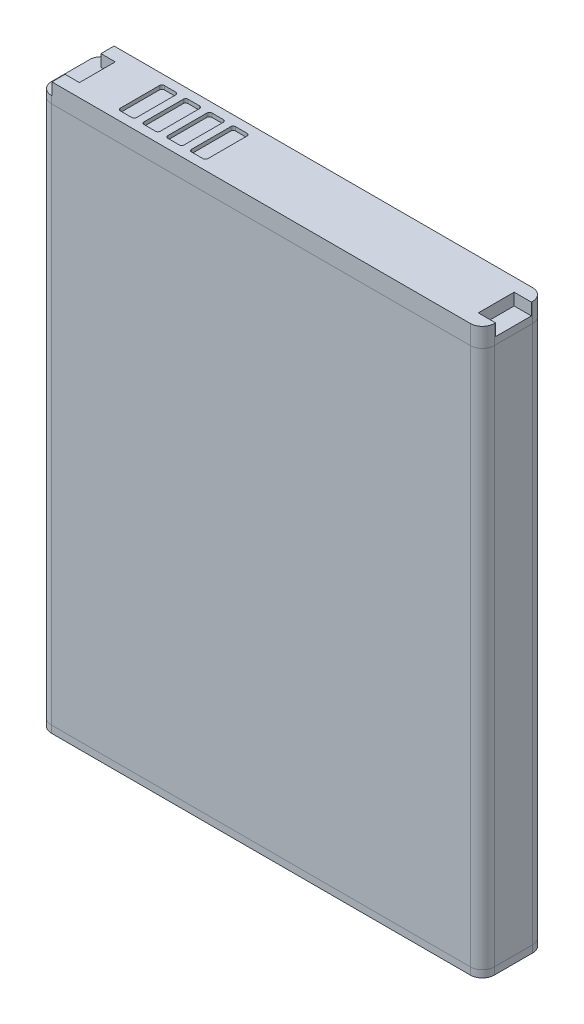
SolidWorks part; units mm, degrees
ref_plane "Front Plane" through (0, 0, 0) normal (0, 0, 1) x (1, 0, 0)
ref_plane "Top Plane" through (0, 0, 0) normal (0, 1, 0) x (1, 0, 0)
ref_plane "Right Plane" through (0, 0, 0) normal (1, 0, 0) x (0, 0, -1)
sketch "Sketch1" plane through (0, 0, 0) normal (0, 1, 0) x (1, 0, 0)
  line L1 (-23.15, -3.25) -> (23.15, -3.25)
  line L2 (-23.15, -3.25) -> (-23.15, 3.25)
  line L3 (-23.15, 3.25) -> (23.15, 3.25)
  line L4 (23.15, -3.25) -> (23.15, 3.25)
  line L5 (-23.15, -3.25) -> (23.15, 3.25) construction
  line L6 (-23.15, 3.25) -> (23.15, -3.25) construction
  point P0 (0, 0)
  dimension "D1" = 6.5
  dimension "D2" = 46.3
extrude "Boss-Extrude1" add sketch "Sketch1" along normal blind 59
fillet "Fillet1" radius 1.25 4 edges at (-23.15, 29.5, 3.25) (-23.15, 29.5, -3.25) (23.15, 29.5, -3.25) (23.15, 29.5, 3.25)
sketch "Sketch2" plane through (0, 59, 0) normal (0, 1, 0) x (1, 0, 0)
  line L0 (0, 0) -> (0, 3.25) construction
  line L1 (21.9, 3.25) -> (-21.9, 3.25) construction
  line L2 (23.15, -2) -> (23.15, 2) construction
  line L3 (21.35, -1.875) -> (23.15, -1.875)
  line L4 (21.35, -1.875) -> (21.35, 1.875)
  line L5 (21.35, 1.875) -> (23.15, 1.875)
  line L6 (23.15, -1.875) -> (23.15, 1.875)
  line L7 (21.35, -1.875) -> (23.15, 1.875) construction
  line L8 (21.35, 1.875) -> (23.15, -1.875) construction
  line L9 (-21.85, 3.25) -> (-21.85, 1.875)
  line L10 (-21.85, 1.875) -> (-20.35, 1.875)
  line L11 (-20.35, 1.875) -> (-20.35, 0)
  line L12 (-20.35, 0) -> (-20.35, -1.875)
  line L13 (-20.35, -1.875) -> (-21.85, -1.875)
  line L14 (-21.85, -1.875) -> (-21.85, -3.25)
  line L15 (-21.9, -3.25) -> (21.9, -3.25) construction
  line L16 (-23.15, 2) -> (-23.15, -2) construction
  line L17 (-21.9, -3.25) -> (-21.85, -3.25)
  line L18 (-23.15, 2) -> (-23.15, -2)
  line L19 (21.9, 3.25) -> (0, 3.25)
  line L20 (-21.85, 3.25) -> (-21.9, 3.25)
  arc A0 (-23.15, -2) -> (-21.9, -3.25) centre (-21.9, -2) ccw construction
  arc A1 (-21.9, 3.25) -> (-23.15, 2) centre (-21.9, 2) ccw construction
  arc A2 (-23.15, -2) -> (-21.9, -3.25) centre (-21.9, -2) ccw
  arc A3 (-21.9, 3.25) -> (-23.15, 2) centre (-21.9, 2) ccw
  point P4 (0, 0)
  point P5 (22.25, 0)
  point P23 (0, 0)
  point P25 (0, 0)
  line M5 (-23.15, 2) -> (-23.15, -2)
  arc M6 (-23.15, -2) -> (-21.9, -3.25) centre (-21.9, -2) ccw
  line M7 (-21.9, -3.25) -> (21.9, -3.25)
  arc M8 (21.9, -3.25) -> (23.15, -2) centre (21.9, -2) ccw
  line M9 (23.15, -2) -> (23.15, 2)
  arc M10 (23.15, 2) -> (21.9, 3.25) centre (21.9, 2) ccw
  line M11 (21.9, 3.25) -> (-21.9, 3.25)
  arc M12 (-21.9, 3.25) -> (-23.15, 2) centre (-21.9, 2) ccw
  dimension "D1" = 3.75
  dimension "D2" = 1.8
  dimension "D3" = 2.8
  dimension "D4" = 1.3
extrude "Cut-Extrude1" cut sketch "Sketch2" against normal blind 1.25 contours L5 L4 L3 M8 M9 M10 | L14 L13 L12 L11 L10 L9 M11 M12 M5 M6 M7
sketch "Sketch3" plane through (0, 59, 0) normal (0, 1, 0) x (1, 0, 0)
  line L0 (-23.15, 2) -> (-23.15, -2) construction
  line L1 (-15.9, -2.3) -> (-14.2, -2.3)
  line L2 (-15.9, -2.3) -> (-15.9, 2.3)
  line L3 (-15.9, 2.3) -> (-14.2, 2.3)
  line L4 (-14.2, -2.3) -> (-14.2, 2.3)
  line L5 (-15.9, -2.3) -> (-14.2, 2.3) construction
  line L6 (-15.9, 2.3) -> (-14.2, -2.3) construction
  line L7 (-11.7167, -2.3) -> (-11.7167, 2.3)
  line L8 (-13.4167, 2.3) -> (-11.7167, 2.3)
  line L9 (-13.4167, -2.3) -> (-13.4167, 2.3)
  line L10 (-13.4167, -2.3) -> (-11.7167, -2.3)
  line L11 (-9.2333, -2.3) -> (-9.2333, 2.3)
  line L12 (-10.9333, 2.3) -> (-9.2333, 2.3)
  line L13 (-10.9333, -2.3) -> (-10.9333, 2.3)
  line L14 (-10.9333, -2.3) -> (-9.2333, -2.3)
  line L15 (-6.75, -2.3) -> (-6.75, 2.3)
  line L16 (-8.45, 2.3) -> (-6.75, 2.3)
  line L17 (-8.45, -2.3) -> (-8.45, 2.3)
  line L18 (-8.45, -2.3) -> (-6.75, -2.3)
  point P0 (-15.05, 0)
  dimension "D1" = 4.6
  dimension "D2" = 1.7
  dimension "D3" = 7.25
  dimension "D5" = 9.15
  dimension "D4" = 4
extrude "Cut-Extrude2" cut sketch "Sketch3" against normal blind 0.4
fillet "Fillet2" radius 0.25 16 edges at (-8.45, 58.8, 2.3) (-6.75, 58.8, 2.3) (-6.75, 58.8, -2.3) (-8.45, 58.8, -2.3) (-10.9333, 58.8, 2.3) (-9.2333, 58.8, 2.3) (-9.2333, 58.8, -2.3) (-10.9333, 58.8, -2.3) (-13.4167, 58.8, 2.3) (-11.7167, 58.8, 2.3) (-11.7167, 58.8, -2.3) (-13.4167, 58.8, -2.3) (-15.9, 58.8, -2.3) (-15.9, 58.8, 2.3) (-14.2, 58.8, 2.3) (-14.2, 58.8, -2.3)
sketch "Sketch4" plane through (0, 0, 3.25) normal (0, 0, 1) x (1, 0, 0)
  line L0 (23.15, 57) -> (-23.15, 57)
  line L1 (23.15, 59) -> (23.15, 0) construction
  line L2 (-23.15, 0) -> (-23.15, 57.75) construction
  line L3 (-23.15, 0.75) -> (23.15, 0.75)
  line L4 (-21.85, 59) -> (21.9, 59) construction
  line L5 (-21.9, 0) -> (21.9, 0) construction
  dimension "D1" = 2
  dimension "D2" = 0.75
split line "Split Line1"
